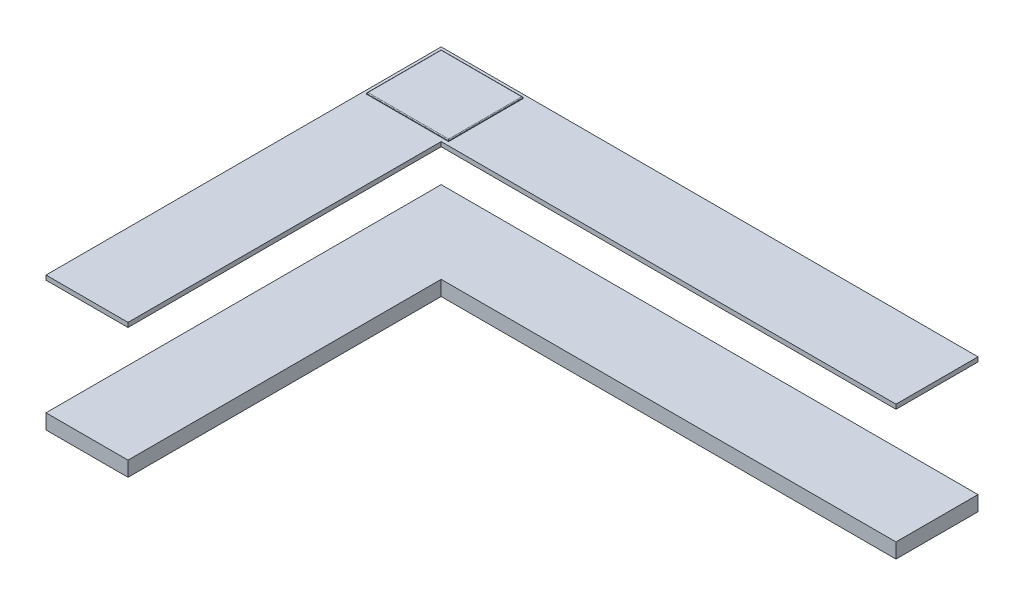
SolidWorks part; units mm, degrees
material "AISI 1020"
ref_plane "Front Plane" through (0, 0, 0) normal (0, 0, 1) x (1, 0, 0)
ref_plane "Top Plane" through (0, 0, 0) normal (0, 1, 0) x (1, 0, 0)
ref_plane "Right Plane" through (0, 0, 0) normal (1, 0, 0) x (0, 0, -1)
sketch "Sketch1" plane through (0, 0, 0) normal (0, 1, 0) x (1, 0, 0)
  line L0 (2163.6943, 907.8775) -> (-1436.3057, 907.8775)
  line L1 (-886.3057, -1742.1225) -> (-1436.3057, -1742.1225)
  line L2 (-886.3057, 357.8775) -> (2163.6943, 357.8775)
  line L3 (2163.6943, 907.8775) -> (2163.6943, 357.8775)
  line L4 (-1436.3057, 907.8775) -> (-1436.3057, -1742.1225)
  line L5 (-886.3057, -1742.1225) -> (-886.3057, 357.8775)
  dimension "D1" = 3600
  dimension "D2" = 2650
  dimension "D3" = 550
  dimension "D4" = 550
extrude "Boss-Extrude1" add sketch "Sketch1" along normal blind 100
ref_plane "Plane1" through (0, 870, 0) normal (0, 1, 0) x (1, 0, 0)
sketch "Sketch11" plane through (0, 870, 0) normal (0, 1, 0) x (1, 0, 0)
  line L0 (-886.3057, 357.8775) -> (-886.3057, -1742.1225)
  line L1 (-886.3057, -1742.1225) -> (-1436.3057, -1742.1225)
  line L2 (-1436.3057, -1742.1225) -> (-1436.3057, 907.8775)
  line L3 (-1436.3057, 907.8775) -> (2163.6943, 907.8775)
  line L4 (2163.6943, 907.8775) -> (2163.6943, 357.8775)
  line L5 (2163.6943, 357.8775) -> (-886.3057, 357.8775)
  dimension "D1" = 2100
  dimension "D2" = 550
  dimension "D3" = 2650
  dimension "D4" = 3600
extrude "Boss-Extrude8" add sketch "Sketch11" along normal blind 30 separate body
sketch "Sketch13" plane through (0, 900, 0) normal (0, 1, 0) x (1, 0, 0)
  line L0 (-1436.3057, -1742.1225) -> (-886.3057, -1742.1225) construction
  line L1 (-911.3057, -1241.1225) -> (-912.3057, -1241.1225)
  line L2 (-911.3057, -1241.1225) -> (-911.3057, -1242.1225)
  line L3 (-911.3057, -1242.1225) -> (-912.3057, -1242.1225)
  line L4 (-912.3057, -1241.1225) -> (-912.3057, -1242.1225)
  line L5 (1763.6943, 383.8775) -> (1762.6943, 383.8775)
  line L6 (1763.6943, 383.8775) -> (1763.6943, 382.8775)
  line L7 (1763.6943, 382.8775) -> (1762.6943, 382.8775)
  line L8 (1762.6943, 383.8775) -> (1762.6943, 382.8775)
  line L9 (2163.6943, 357.8775) -> (2163.6943, 907.8775) construction
  line L10 (-886.3057, -1742.1225) -> (-886.3057, 357.8775) construction
  line L11 (-886.3057, 357.8775) -> (2163.6943, 357.8775) construction
  dimension "D1" = 1
  dimension "D2" = 1
  dimension "D3" = 1
  dimension "D4" = 1
  dimension "D5" = 500
  dimension "D6" = 25
  dimension "D7" = 400
  dimension "D8" = 25
extrude "Cut-Extrude1" cut sketch "Sketch13" against normal blind 30
sketch "Sketch14" plane through (0, 900, 0) normal (0, 1, 0) x (1, 0, 0)
  line L0 (2163.6943, 907.8775) -> (-1436.3057, 907.8775) construction
  line L1 (-1411.3057, 882.8775) -> (-861.3057, 882.8775)
  line L2 (-1411.3057, 882.8775) -> (-1411.3057, 382.8775)
  line L3 (-1411.3057, 382.8775) -> (-861.3057, 382.8775)
  line L4 (-861.3057, 882.8775) -> (-861.3057, 382.8775)
  line L5 (-1436.3057, 907.8775) -> (-1436.3057, -1742.1225) construction
  dimension "D1" = 500
  dimension "D2" = 550
  dimension "D3" = 25
  dimension "D4" = 25
extrude "Boss-Extrude9" add sketch "Sketch14" along normal blind 10
fillet "Fillet1" radius 5 4 edges at (-1136.3057, 910, -882.8775) (-861.3057, 910, -632.8775) (-1136.3057, 910, -382.8775) (-1411.3057, 910, -632.8775)
sketch "Sketch16" plane through (0, 910, 0) normal (0, 1, 0) x (1, 0, 0)
  line L0 (-866.3057, 877.8775) -> (-1406.3057, 877.8775) construction
  line L1 (-898.6098, 829.7546) -> (-934.5516, 829.7546)
  line L2 (-898.6098, 829.7546) -> (-898.6098, 687.8603)
  line L3 (-898.6098, 687.8603) -> (-934.5516, 687.8603)
  line L4 (-934.5516, 829.7546) -> (-934.5516, 687.8603)
  line L5 (-1406.3057, 387.8775) -> (-866.3057, 387.8775) construction
  line L6 (-1406.3057, 877.8775) -> (-1406.3057, 387.8775) construction
  circle A0 centre (-1270.3552, 542.8775) radius 59.0879
  circle A1 centre (-1044.0387, 542.8775) radius 90.657
  circle A2 centre (-1044.0387, 542.8775) radius 67.519
  circle A3 centre (-1044.0387, 727.8775) radius 56.1791
  circle A4 centre (-916.5807, 796.3073) radius 7.3291
  circle A5 centre (-916.5807, 771.3073) radius 7.3
  circle A6 centre (-916.5807, 746.3073) radius 7.3
  circle A7 centre (-916.5807, 721.3073) radius 7.3
  circle A8 centre (-1270.3552, 727.8775) radius 69.8722
  dimension "D4" = 33.4474
  dimension "D1" = 25
  dimension "D2" = 25
  dimension "D3" = 25
  dimension "D5" = 33.447
  dimension "D6" = 48.1229
  dimension "D7" = 150
  dimension "D8" = 155
  dimension "D9" = 155
  dimension "D10" = 150
  dimension "D11" = 135.9505
  dimension "D12" = 135.9505
  dimension "D13" = 362.267
  dimension "D14" = 362.267
  dimension "D15" = 471.7541
  dimension "D16" = 507.6959
  dimension "D17" = 17.9709
  dimension "D18" = 17.9709
